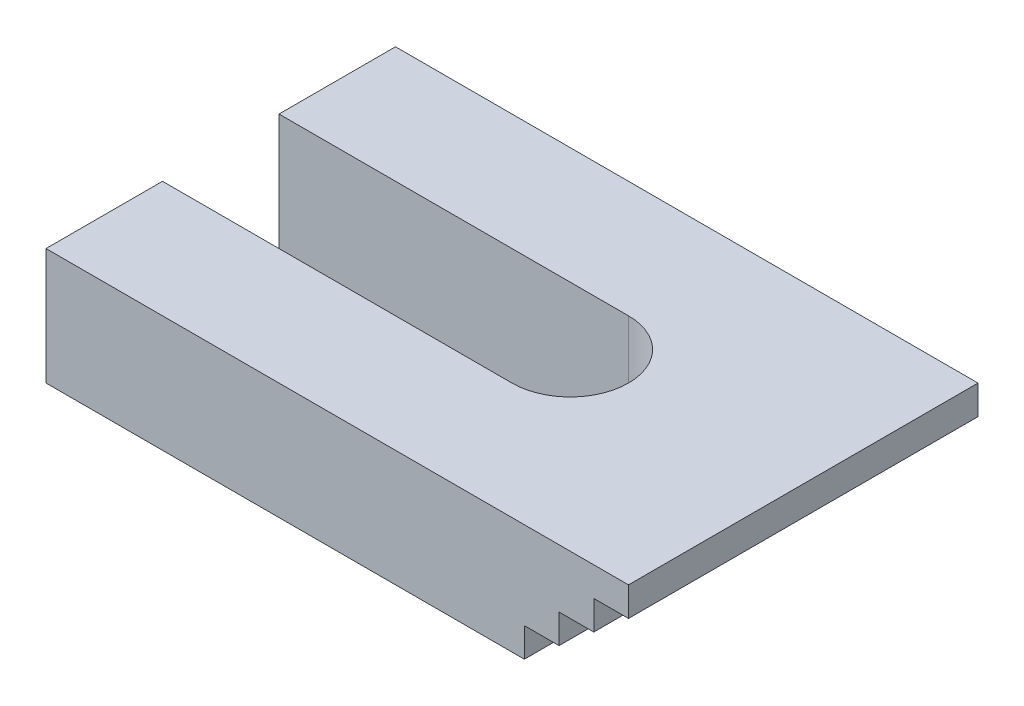
SolidWorks part; units mm, degrees
ref_plane "Plan de face" through (0, 0, 0) normal (0, 0, 1) x (1, 0, 0)
ref_plane "Plan de dessus" through (0, 0, 0) normal (0, 1, 0) x (1, 0, 0)
ref_plane "Plan de droite" through (0, 0, 0) normal (1, 0, 0) x (0, 0, -1)
sketch "Esquisse1" plane through (0, 0, 0) normal (0, 0, 1) x (1, 0, 0)
  line L2 (-8.4759, -4.7717) -> (-8.4759, -2.2717)
  line L5 (-2.5172, 0.2283) -> (-2.5172, 2.7283)
  line L6 (-5.4966, -2.2717) -> (-5.4966, 0.2283)
  line L7 (0.4628, 2.7283) -> (0.4628, 5.2283)
  line L9 (-2.5172, 2.7283) -> (0.4628, 2.7283)
  line L10 (-8.4759, -2.2717) -> (-5.4966, -2.2717)
  line L11 (0.4628, 5.2283) -> (-49.5372, 5.2283)
  line L13 (-8.4759, -4.7717) -> (-49.5372, -4.7717)
  line L14 (-49.5372, 5.2283) -> (-49.5372, -4.7717)
  line L15 (-5.4966, 0.2283) -> (-2.5172, 0.2283)
  dimension "D1" = 2.9794
  dimension "D2" = 2.9794
  dimension "D3" = 2.98
  dimension "D4" = 50
extrude "Boss.-Extru.1" add sketch "Esquisse1" along normal blind 30
sketch "Esquisse2" plane through (0, -4.7717, 0) normal (0, -1, 0) x (1, 0, 0)
  line L0 (-49.5372, 15) -> (-17.7781, 15) construction
  line L1 (-49.5372, 30) -> (-49.5372, 0) construction
  line L2 (-19.5372, 20) -> (-49.5372, 20)
  line L3 (-19.5372, 10) -> (-49.5372, 10)
  arc A0 (-19.5372, 10) -> (-19.5372, 20) centre (-19.5372, 15) ccw
  dimension "D1" = 30
extrude "Enlèv. mat.-Extru.1" cut sketch "Esquisse2" against normal through all flip side to cut
